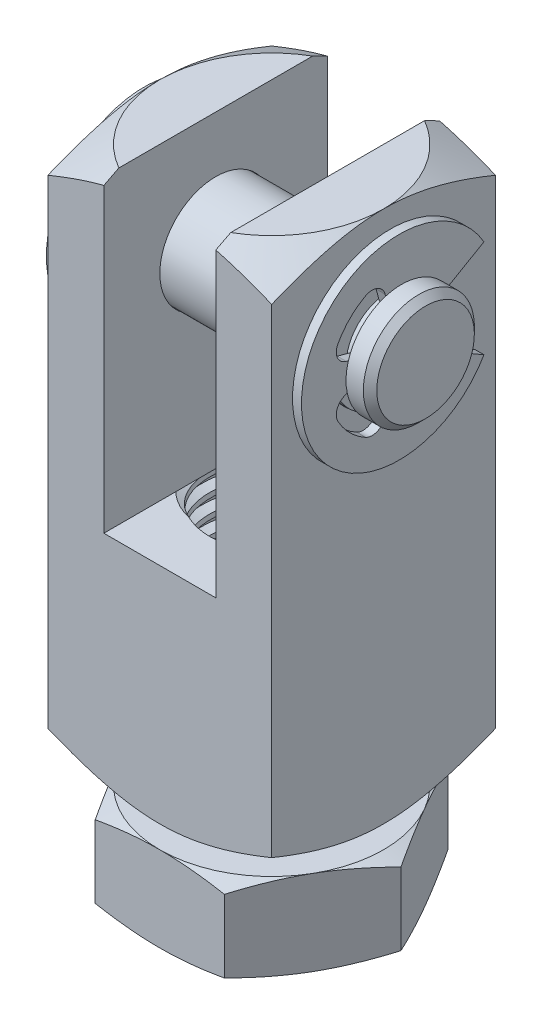
SolidWorks part; units mm, degrees
ref_plane "Front" through (0, 0, 0) normal (0, 0, 1) x (1, 0, 0)
ref_plane "Top" through (0, 0, 0) normal (0, 1, 0) x (1, 0, 0)
ref_plane "Right" through (0, 0, 0) normal (1, 0, 0) x (0, 0, -1)
sketch "Sketch1" plane through (0, 0, 0) normal (0, 0, 1) x (1, 0, 0)
  line L1 (-6.35, 0) -> (6.35, 0)
  line L2 (-6.35, 0) -> (-6.35, 30.226)
  line L3 (-6.35, 30.226) -> (6.35, 30.226)
  line L4 (6.35, 0) -> (6.35, 30.226)
  dimension "Height" = 30.226
  dimension "Width" = 12.7
extrude "Extrude1" add sketch "Sketch1" along normal mid plane 12.7
sketch "Sketch2" plane through (0, 0, 0) normal (0, 0, 1) x (1, 0, 0)
  line L0 (-6.35, 30.226) -> (6.35, 30.226) construction
  line L1 (-3.175, 30.226) -> (3.175, 30.226)
  line L2 (-3.175, 30.226) -> (-3.175, 12.7)
  line L3 (-3.175, 12.7) -> (3.175, 12.7)
  line L4 (3.175, 30.226) -> (3.175, 12.7)
  line L5 (0, 0) -> (0, 12.7) construction
  dimension "Slot Width" = 6.35
  dimension "Slot Height" = 17.526
extrude "Cut-Extrude1" cut sketch "Sketch2" against normal through all and the other way through all
sketch "Sketch9" plane through (0, 0, 0) normal (0, 0, 1) x (1, 0, 0)
  line L0 (6.35, 0) -> (6.35, 30.226) construction
  line L1 (-6.35, 27.051) -> (6.35, 27.051)
  line L2 (-6.35, 27.051) -> (-6.35, 23.876)
  line L3 (-6.35, 23.876) -> (6.35, 23.876)
  line L4 (6.35, 27.051) -> (6.35, 23.876)
  line L5 (-6.35, 0) -> (-6.35, 30.226) construction
  line L6 (-6.35, 30.226) -> (6.35, 30.226) construction
  line L7 (-6.35, 23.876) -> (-9.525, 23.876) construction
  dimension "Pin Dist" = 6.35
  dimension "Pin Dia" = 6.35
revolve "Cut-Revolve3" cut sketch "Sketch9" angle 360 about L7
sketch "Sketch4" plane through (0, 30.226, 0) normal (0, 1, 0) x (-1, 0, 0)
  circle A0 centre (0, 0) radius 6.35
extrude "Cut-Extrude3" cut sketch "Sketch4" against normal through all draft 60 flip side to cut
sketch "Sketch5" plane through (0, 0, 0) normal (0, 1, 0) x (1, 0, 0)
  circle A0 centre (0, 0) radius 6.35 construction
  circle A1 centre (0, 0) radius 6.35
extrude "Cut-Extrude4" cut sketch "Sketch5" along normal through all draft 60 flip side to cut
sketch "Sketch6" plane through (0, 0, 0) normal (0, 0, 1) x (1, 0, 0)
  line L0 (0, 0) -> (0, 12.7) construction
  line L1 (0, 0) -> (3.9688, 0)
  line L2 (0, 0) -> (0, 12.7)
  line L3 (0, 12.7) -> (3.9687, 12.7)
  line L4 (3.9688, 0) -> (3.9687, 12.7)
  line L5 (-3.175, 12.7) -> (3.175, 12.7) construction
  line L6 (0, 0) -> (0, -3.9688) construction
  line L7 (-3.9688, 0) -> (-3.9688, 12.7) construction
  dimension "Thread Dia" = 7.9375
revolve "Revolve1" add sketch "Sketch6" angle 360 about L6
sketch "Sketch7" plane through (0, 0, 0) normal (0, 0, 1) x (1, 0, 0)
  line L0 (-3.9688, 0) -> (3.9688, 0) construction
  line L1 (3.9688, 0) -> (3.9688, 1.0583) construction
  line L2 (3.9688, 1.0583) -> (-3.9688, 0) construction
  line L3 (-3.9688, 0) -> (-3.9862, 0.1311) construction
  line L4 (-3.9862, 0.1311) -> (-4.1086, 1.049)
  line L5 (-4.1086, 1.049) -> (-3.4971, 0.7969)
  line L6 (-3.4971, 0.7969) -> (-3.4621, 0.5347)
  line L7 (-3.4621, 0.5347) -> (-3.9862, 0.1311)
  line L8 (-3.4796, 0.6658) -> (-4.0474, 0.5901) construction
  line L9 (-3.9688, 0) -> (-3.9688, 0.6006) construction
  line L10 (-3.9688, 0.6006) -> (3.9688, 1.6589) construction
  line L11 (3.9688, 1.6589) -> (3.9688, 1.0583) construction
  line L12 (-3.9688, 0) -> (-3.9688, 12.7) construction
  line L13 (-3.9688, 0) -> (3.9688, 0) construction
  line L14 (3.9688, 0) -> (3.9687, 12.7) construction
  line L15 (0.1506, 0) -> (-0.1506, 2.2595) construction
  point P19 (0, 1.1297)
  dimension "D1" = 0.1323
  dimension "D2" = 0.2646
  dimension "D3" = 1.0583
  dimension "Thread Pitch" = 1.0583
  dimension "D4" = 60
revolve "Cut-Revolve1" cut sketch "Sketch7" angle 360 about L15
pattern_linear "LPattern1" count 2 spacing 1.0583 along (0, -1, 0) count 12 spacing 1.0583 along (0, 1, 0) of "Cut-Revolve1"
sketch "Sketch8" plane through (0, 0, 0) normal (0, 0, 1) x (1, 0, 0)
  line L0 (3.9687, 0) -> (0, 2.2914)
  line L1 (0, 2.2914) -> (0, 0)
  line L2 (0, 0) -> (3.9687, 0)
  dimension "D1" = 30
revolve "Cut-Revolve2" cut sketch "Sketch8" angle 360 about L1
combine bodies "Combine1" operation type subtract main body 117 bodies to subtract 116
ref_plane "Plane1" through (0, -1.27, 0) normal (0, 1, 0) x (-1, 0, 0)
sketch "Sketch10" plane through (0, -1.27, 0) normal (0, 1, 0) x (-1, 0, 0)
  line L1 (-7.3323, 0) -> (-3.6662, -6.35)
  line L2 (-3.6662, -6.35) -> (3.6662, -6.35)
  line L3 (3.6662, -6.35) -> (7.3323, 0)
  line L4 (7.3323, 0) -> (3.6662, 6.35)
  line L5 (3.6662, 6.35) -> (-3.6662, 6.35)
  line L6 (-3.6662, 6.35) -> (-7.3323, 0)
  circle A0 centre (0, 0) radius 6.35 construction
  dimension "D1" = 12.7
extrude "Extrude2" add sketch "Sketch10" against normal blind 4.826 separate body
sketch "Sketch11" plane through (0, 0, 0) normal (0, 0, 1) x (1, 0, 0)
  line L0 (6.35, -1.27) -> (7.3323, -1.27)
  line L1 (7.3323, -1.27) -> (7.3323, -1.6275)
  line L2 (7.3323, -1.6275) -> (6.35, -1.27)
  line L3 (6.35, -6.096) -> (7.3323, -6.096)
  line L4 (7.3323, -6.096) -> (7.3323, -5.7385)
  line L5 (7.3323, -5.7385) -> (6.35, -6.096)
  line L6 (6.35, -1.27) -> (6.35, -6.096) construction
  line L7 (7.3323, -6.096) -> (7.3323, -1.27) construction
  line L8 (3.6662, -6.096) -> (7.3323, -6.096) construction
  line L11 (6.35, -1.27) -> (0, -1.27) construction
  line L12 (6.35, -1.27) -> (-6.35, -1.27) construction
  line L13 (0, -1.27) -> (0, -6.096) construction
  line L14 (0, -6.096) -> (6.35, -6.096) construction
  dimension "D1" = 20
revolve "Cut-Revolve4" cut sketch "Sketch11" angle 360 about L13
sketch "Sketch12" plane through (0, 0, 0) normal (0, 0, 1) x (1, 0, 0)
  line L0 (3.9688, 0) -> (3.9687, 12.7) construction
  line L1 (0, -1.27) -> (3.9688, -1.27)
  line L2 (0, -1.27) -> (0, -6.096)
  line L3 (0, -6.096) -> (3.9687, -6.096)
  line L4 (3.9688, -1.27) -> (3.9687, -6.096)
  line L5 (0, 0) -> (0, 12.7) construction
  line L6 (6.35, -1.27) -> (0, -1.27) construction
  line L7 (0, -6.096) -> (6.35, -6.096) construction
  line L8 (0, -6.096) -> (0, 0) construction
  line L9 (-3.9688, -1.27) -> (-3.9687, -6.096) construction
revolve "Revolve2" add sketch "Sketch12" angle 360 about L2
sketch "Sketch13" plane through (0, 0, 0) normal (0, 0, 1) x (1, 0, 0)
  line L0 (-3.9688, -6.096) -> (3.9688, -6.096) construction
  line L1 (3.9688, -6.096) -> (3.9688, -5.0377) construction
  line L2 (3.9688, -5.0377) -> (-3.9688, -6.096) construction
  line L3 (-3.9688, -6.096) -> (-3.9862, -5.9649) construction
  line L4 (-3.9862, -5.9649) -> (-4.1086, -5.047)
  line L5 (-4.1086, -5.047) -> (-3.4971, -5.2991)
  line L6 (-3.4971, -5.2991) -> (-3.4621, -5.5613)
  line L7 (-3.4621, -5.5613) -> (-3.9862, -5.9649)
  line L8 (-3.4796, -5.4302) -> (-4.0474, -5.5059) construction
  line L9 (-3.9688, -6.096) -> (-3.9688, -5.4954) construction
  line L10 (-3.9688, -5.4954) -> (3.9688, -4.4371) construction
  line L11 (3.9688, -4.4371) -> (3.9688, -5.0377) construction
  line L15 (-3.9688, -1.27) -> (-3.9687, -6.096) construction
  line L16 (0, -6.096) -> (3.9687, -6.096) construction
  line L17 (3.9688, -1.27) -> (3.9687, -6.096) construction
  line L18 (0.1506, -6.096) -> (-0.1506, -3.8365) construction
  point P19 (0, -4.9663)
  dimension "D1" = 0.1323
  dimension "D2" = 0.2646
  dimension "D3" = 1.0583
  dimension "D4" = 60
  dimension "D5" = 1.0583
revolve "Cut-Revolve5" cut sketch "Sketch13" angle 360 about L18
pattern_linear "LPattern3" count 2 spacing 1.0583 along (0, -1, 0) count 5 spacing 1.0583 along (0, 1, 0) of "Cut-Revolve5"
sketch "Sketch14" plane through (0, -1.27, 0) normal (0, 1, 0) x (-1, 0, 0)
  circle A0 centre (0, 0) radius 3.9688
extrude "Cut-Extrude5" cut sketch "Sketch14" against normal through all draft 60
sketch "Sketch15" plane through (0, -6.096, 0) normal (0, -1, 0) x (1, 0, 0)
  circle A0 centre (0, 0) radius 3.9688 construction
  circle A1 centre (0, 0) radius 3.9688
extrude "Cut-Extrude6" cut sketch "Sketch15" against normal through all draft 60
combine bodies "Combine2" operation type subtract main body 126 bodies to subtract 124
sketch "Sketch16" plane through (0, 0, 0) normal (0, 0, 1) x (1, 0, 0)
  line L0 (0, 0) -> (0, 27.0256) construction
  line L1 (-8.7312, 27.0256) -> (-7.366, 27.0256)
  line L2 (8.7312, 27.0256) -> (8.7312, 23.876)
  line L3 (8.7312, 23.876) -> (-8.7312, 23.876)
  line L4 (-8.7312, 23.876) -> (-8.7312, 27.0256)
  line L5 (-6.604, 27.0256) -> (6.604, 27.0256)
  line L6 (8.7312, 23.876) -> (11.8808, 23.876) construction
  line L7 (-6.35, 27.051) -> (6.35, 27.051) construction
  line L8 (-6.35, 23.876) -> (-9.525, 23.876) construction
  line L10 (7.366, 27.0256) -> (8.7312, 27.0256)
  line L11 (-7.366, 27.0256) -> (-7.366, 26.2636)
  line L16 (-7.366, 26.2636) -> (-6.604, 26.2636)
  line L17 (-6.604, 27.0256) -> (-6.604, 26.2636)
  line L18 (-6.35, 28.7074) -> (-6.35, 1.5186) construction
  line L19 (6.604, 27.0256) -> (6.604, 26.2636)
  line L20 (6.604, 26.2636) -> (7.366, 26.2636)
  line L21 (7.366, 27.0256) -> (7.366, 26.2636)
  point P23 (-6.985, 26.2636)
  dimension "D1" = 0.762
  dimension "Pin Length" = 17.4625
  dimension "D2" = 0.0254
  dimension "D3" = 0.254
  dimension "D4" = 0.762
revolve "Revolve3" add sketch "Sketch16" angle 360 about L6
chamfer "Chamfer1" distance 0.381 angle 45 2 edges at (8.7312, 20.7264, 0) (-8.7313, 20.7264, 0)
ref_plane "Plane2" through (-6.985, 0, 0) normal (1, 0, 0) x (0, 0, -1)
sketch "Sketch17" plane through (-6.985, 0, 0) normal (1, 0, 0) x (0, 0, -1)
  line L0 (0, 23.876) -> (4.4884, 23.876) construction
  line L1 (2.0677, 25.0698) -> (4.8064, 26.651)
  line L2 (2.0677, 22.6822) -> (4.8064, 21.1011)
  line L3 (0, 23.876) -> (-3.3536, 27.2296) construction
  line L4 (0, 23.876) -> (0, 27.0256) construction
  line L5 (-0.618, 26.1822) -> (-0.8062, 26.8848)
  line L6 (-2.3062, 24.494) -> (-3.0088, 24.6822)
  line L7 (-0.618, 21.5698) -> (-0.8062, 20.8672)
  line L8 (-2.3062, 23.258) -> (-3.0088, 23.0698)
  arc A0 (-2.3062, 24.494) -> (-2.3062, 23.258) centre (0, 23.876) ccw
  arc A1 (4.8064, 26.651) -> (4.8064, 21.1011) centre (0, 23.876) ccw
  arc A2 (-1.9087, 27.3556) -> (-3.4796, 25.7847) centre (0, 23.876) ccw
  arc A3 (-3.0088, 24.6822) -> (-3.4796, 25.7847) centre (-2.8115, 25.4182) cw
  arc A4 (-1.9087, 27.3556) -> (-0.8062, 26.8848) centre (-1.5422, 26.6875) cw
  arc A5 (-1.9087, 20.3964) -> (-0.8062, 20.8672) centre (-1.5422, 21.0645) ccw
  arc A6 (-1.9087, 20.3964) -> (-3.4796, 21.9673) centre (0, 23.876) cw
  arc A7 (-3.0088, 23.0698) -> (-3.4796, 21.9673) centre (-2.8115, 22.3338) ccw
  arc A8 (-0.618, 21.5698) -> (2.0677, 22.6822) centre (0, 23.876) ccw
  arc A9 (2.0677, 25.0698) -> (-0.618, 26.1822) centre (0, 23.876) ccw
  point P9 (3.437, 25.8604)
  dimension "D2" = 5.5499
  dimension "D6" = 0.762
  dimension "D1" = 60
  dimension "D3" = 45
  dimension "D4" = 60
  dimension "D5" = 30
extrude "Extrude3" add sketch "Sketch17" along normal mid plane 0.508
mirror "Mirror1" about plane through (0, 0, 0) normal (1, 0, 0) of "Extrude3"
equation "\"D1@Extrude1\"=\"Width@Sketch1\""
equation "\"D1@Sketch7\"=\"Thread Pitch@Sketch7\"/8"
equation "\"D2@Sketch7\"=\"Thread Pitch@Sketch7\"/4"
equation "\"D3@Sketch7\"=\"Thread Pitch@Sketch7\""
equation "\"D3@LPattern1\"=\"Thread Pitch@Sketch7\""
equation "\"D4@LPattern1\"=\"Thread Pitch@Sketch7\""
equation "\"D2@LPattern1\"=(\"Height@Sketch1\"-\"Slot Height@Sketch2\")/\"Thread Pitch@Sketch7\""
equation "\"D1@Sketch10\"=\"Width@Sketch1\""
equation "\"D3@Sketch13\"=\"Thread Pitch@Sketch7\""
equation "\"D1@Sketch13\"=\"D1@Sketch7\""
equation "\"D2@Sketch13\"=\"D2@Sketch7\""
equation "\"D5@Sketch13\"=\"D3@Sketch7\""
equation "\"D4@LPattern3\"=\"Thread Pitch@Sketch7\""
equation "\"D3@LPattern3\"=\"Thread Pitch@Sketch7\""
equation " \"D2@LPattern3\"=\"Nut Height@Extrude2\"/\"Thread Pitch@Sketch7\""
